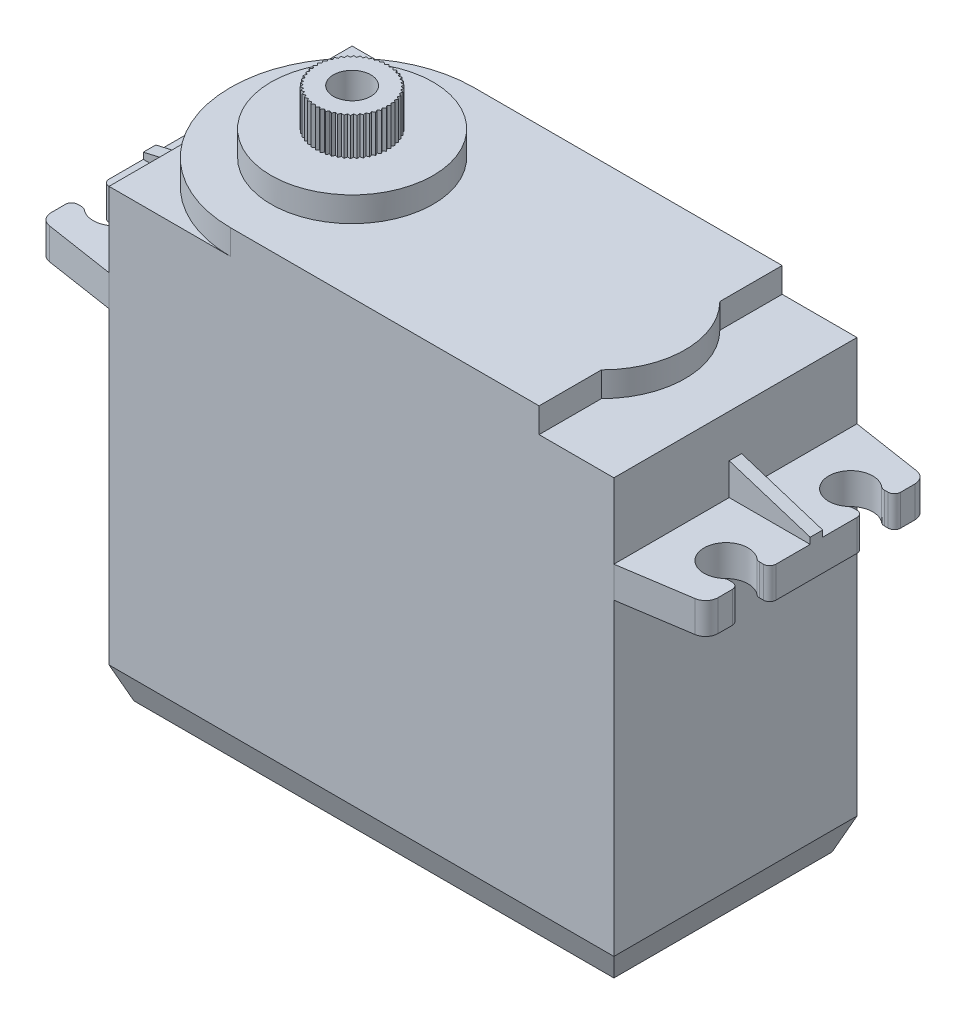
SolidWorks part; units mm, degrees
ref_plane "Front Plane" through (0, 0, 0) normal (0, 0, 1) x (1, 0, 0)
ref_plane "Top Plane" through (0, 0, 0) normal (0, 1, 0) x (1, 0, 0)
ref_plane "Right Plane" through (0, 0, 0) normal (1, 0, 0) x (0, 0, -1)
sketch "Sketch1" plane through (0, 0, 0) normal (0, 1, 0) x (1, 0, 0)
  line L1 (-20.25, -9.75) -> (20.25, -9.75)
  line L2 (-20.25, -9.75) -> (-20.25, 9.75)
  line L3 (-20.25, 9.75) -> (20.25, 9.75)
  line L4 (20.25, -9.75) -> (20.25, 9.75)
  line L5 (-20.25, -9.75) -> (20.25, 9.75) construction
  line L6 (-20.25, 9.75) -> (20.25, -9.75) construction
  point P0 (0, 0)
extrude "Boss-Extrude1" add sketch "Sketch1" along normal blind 35.75
sketch "Sketch2" plane through (0, 35.75, 0) normal (0, 1, 0) x (1, 0, 0)
  line L0 (-26.75, 8.75) -> (-26.75, 6.25)
  line L2 (-26.75, 6.25) -> (-25.75, 6.25)
  line L6 (20.25, 9.75) -> (26.75, 8.75)
  line L7 (20.25, -9.75) -> (26.75, -8.75)
  line L8 (-20.25, -9.75) -> (-26.75, -8.75)
  line L9 (-26.75, 8.75) -> (-20.25, 9.75)
  line L10 (-20.25, 9.75) -> (-20.25, -9.75)
  line L11 (20.25, -9.75) -> (20.25, 9.75)
  line L12 (-25.75, 3.75) -> (-26.75, 3.75)
  line L13 (-26.75, -8.75) -> (-26.75, -6.25)
  line L14 (-26.75, -6.25) -> (-25.75, -6.25)
  line L15 (-25.75, -3.75) -> (-26.75, -3.75)
  line L16 (-26.75, -3.75) -> (-26.75, 3.75)
  line L17 (26.75, 8.75) -> (26.75, 6.25)
  line L18 (26.75, 6.25) -> (25.75, 6.25)
  line L19 (25.75, 3.75) -> (26.75, 3.75)
  line L20 (26.75, 3.75) -> (26.75, -3.75)
  line L21 (26.75, -3.75) -> (25.75, -3.75)
  line L22 (25.75, -6.25) -> (26.75, -6.25)
  line L23 (26.75, -6.25) -> (26.75, -8.75)
  arc A4 (-25.75, 6.25) -> (-25.75, 3.75) centre (-24.5, 5) cw
  arc A5 (-25.75, -3.75) -> (-25.75, -6.25) centre (-24.5, -5) cw
  arc A6 (25.75, -6.25) -> (25.75, -3.75) centre (24.5, -5) cw
  arc A7 (25.75, 3.75) -> (25.75, 6.25) centre (24.5, 5) cw
extrude "Boss-Extrude2" add sketch "Sketch2" against normal blind 2.5 from offset 6 offset against normal yes
sketch "Sketch3" plane through (0, 0, 0) normal (0, 0, 1) x (1, 0, 0)
  line L0 (-26.75, 29.75) -> (-26.75, 30.25)
  line L1 (-20.25, 29.75) -> (-20.25, 31.75)
  line L2 (-20.25, 35.75) -> (-20.25, 29.75) construction
  line L3 (-26.75, 30.25) -> (-20.25, 31.75)
  line L4 (-20.25, 29.75) -> (-26.75, 29.75)
  line L5 (20.25, 29.75) -> (20.25, 32.3089)
  line L6 (20.25, 35.75) -> (20.25, 29.75) construction
  line L7 (26.75, 29.75) -> (26.75, 30.25)
  line L8 (26.75, 30.25) -> (20.25, 32.3089)
  line L9 (20.25, 29.75) -> (26.75, 29.75)
extrude "Boss-Extrude3" add sketch "Sketch3" along normal blind 0.5 and the other way blind 0.5
fillet "Fillet1" radius 1 4 edges at (26.75, 28.5, -8.75) (26.75, 28.5, 8.75) (-26.75, 28.5, -8.75) (-26.75, 28.5, 8.75)
fillet "Fillet3" radius 0.5 16 edges at (-25.75, 28.5, 3.75) (-26.75, 28.5, 3.75) (-25.75, 28.5, -6.25) (-26.75, 28.5, -6.25) (-25.75, 28.5, -3.75) (-26.75, 28.5, -3.75) (-26.75, 28.5, 6.25) (-25.75, 28.5, 6.25) (26.75, 28.5, -3.75) (25.75, 28.5, -3.75) (26.75, 28.5, 6.25) (25.75, 28.5, 6.25) (26.75, 28.5, 3.75) (25.75, 28.5, 3.75) (26.75, 28.5, -6.25) (25.75, 28.5, -6.25)
chamfer "Chamfer2" distance 1 distance2 2.5 4 edges at (-20.25, 0, 0) (0, 0, -9.75) (20.25, 0, 0) (0, 0, 9.75)
sketch "Sketch4" plane through (0, 35.75, 0) normal (0, 1, 0) x (1, 0, 0)
  line L0 (-10.5, -9.75) -> (14.25, -9.75)
  line L1 (-10.5, 9.75) -> (14.25, 9.75)
  line L2 (20.25, 9.75) -> (-20.25, 9.75) construction
  line L3 (14.25, 9.75) -> (14.25, 4.75)
  line L4 (14.25, -9.75) -> (14.25, -4.75)
  arc A1 (14.25, -4.75) -> (14.25, 4.75) centre (9.5, 0) ccw
  arc A2 (-10.5, -9.75) -> (-10.5, 9.75) centre (-10.5, 0) cw
extrude "Boss-Extrude4" add sketch "Sketch4" along normal blind 2
sketch "Sketch5" plane through (0, 37.75, 0) normal (0, 1, 0) x (1, 0, 0)
  circle A0 centre (-10.5, 0) radius 6.5
extrude "Boss-Extrude5" add sketch "Sketch5" along normal blind 2
sketch "Sketch6" plane through (0, 39.75, 0) normal (0, 1, 0) x (1, 0, 0)
  circle A0 centre (-10.5, 0) radius 2.75
extrude "Boss-Extrude6" add sketch "Sketch6" along normal blind 3
sketch "Sketch7" plane through (0, 42.75, 0) normal (0, 1, 0) x (1, 0, 0)
  circle A0 centre (-10.5, 0) radius 1.5
extrude "Cut-Extrude1" cut sketch "Sketch7" against normal blind 3
sketch "Sketch8" plane through (0, 42.75, 0) normal (0, 1, 0) x (1, 0, 0)
  line L1 (-10.5, 2.95) -> (-10.2921, 2.7421)
  line L2 (-10.5, 2.95) -> (-10.7079, 2.7421)
  line L3 (-10.7079, 2.7421) -> (-10.2921, 2.7421)
  circle A1 centre (-10.5, 0) radius 2.75 construction
extrude "Boss-Extrude7" add sketch "Sketch8" against normal blind 3
pattern_circular "CirPattern1" count 50 over 360 about axis through (-10.5, 0, 0) along (0, 1, 0) of "Boss-Extrude7"
sketch "Sketch9" plane through (-20.25, 0, 0) normal (-1, 0, 0) x (0, 0, 1)
  line L0 (-9.75, 2.5) -> (9.75, 2.5) construction
  line L1 (-3.5, 1) -> (3.5, 1)
  line L2 (-3.5, 1) -> (-3.5, 4)
  line L3 (-3.5, 4) -> (3.5, 4)
  line L4 (3.5, 1) -> (3.5, 4)
  line L5 (-3.5, 1) -> (3.5, 4) construction
  line L6 (-3.5, 4) -> (3.5, 1) construction
  point P0 (0, 2.5)
extrude "Boss-Extrude8" add sketch "Sketch9" along normal blind 5 and the other way blind 3
chamfer "Chamfer4" distance 3.5 distance2 0.25 4 edges at (-25.25, 2.5, -3.5) (-25.25, 1, 0) (-25.25, 2.5, 3.5) (-25.25, 4, 0)
